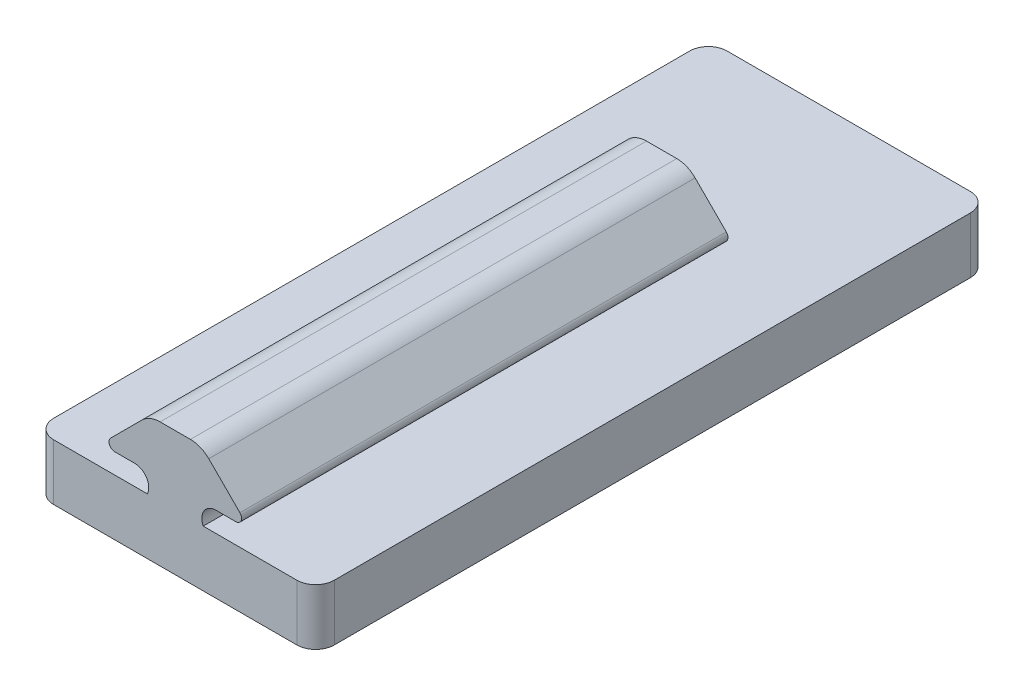
SolidWorks part; units mm, degrees
ref_plane "Front Plane" through (0, 0, 0) normal (0, 0, 1) x (1, 0, 0)
ref_plane "Top Plane" through (0, 0, 0) normal (0, 1, 0) x (1, 0, 0)
ref_plane "Right Plane" through (0, 0, 0) normal (1, 0, 0) x (0, 0, -1)
sketch "Sketch1" plane through (0, 0, 0) normal (0, 1, 0) x (1, 0, 0)
  line L1 (-13, 36) -> (13, 36)
  line L2 (-15, 34) -> (-15, -34)
  line L3 (-13, -36) -> (13, -36)
  line L4 (15, 34) -> (15, -34)
  line L5 (-15, 36) -> (15, -36) construction
  line L6 (-15, -36) -> (15, 36) construction
  arc A0 (13, 36) -> (15, 34) centre (13, 34) cw
  arc A1 (13, -36) -> (15, -34) centre (13, -34) ccw
  arc A2 (-15, -34) -> (-13, -36) centre (-13, -34) ccw
  arc A3 (-13, 36) -> (-15, 34) centre (-13, 34) ccw
  point P0 (0, 0)
  dimension "D1" = 2
  dimension "D2" = 72
  dimension "D3" = 30
extrude "Boss-Extrude1" add sketch "Sketch1" along normal blind 6
sketch "Sketch2" plane through (0, 0, 0) normal (0, 1, 0) x (1, 0, 0)
  line L0 (0, 24) -> (0, -24) construction
  circle A0 centre (0, 24) radius 4
  circle A1 centre (0, -24) radius 4
  point P3 (0, 0)
  dimension "D1" = 8
  dimension "D2" = 48
extrude "Cut-Extrude1" cut sketch "Sketch2" along normal blind 2
sketch "Sketch3" plane through (0, 0, 0) normal (0, 0, 1) x (1, 0, 0)
  line L0 (-5.3171, 5.6) -> (-5.3171, 3.6) construction
  line L1 (-5.3171, 3.6) -> (5.3171, 3.6) construction
  line L2 (5.3171, 3.6) -> (5.3171, 5.6) construction
  line L3 (-4.9167, 5.1447) -> (-4.343, 5.1447)
  line L4 (-4.343, 8.1545) -> (-6.4744, 8.1545)
  line L5 (-6.91, 9.206) -> (-3.5799, 12.5361)
  line L6 (-1.6177, 13.3489) -> (1.6185, 13.3489)
  line L7 (3.5807, 12.5361) -> (6.9108, 9.206)
  line L8 (6.4752, 8.1545) -> (4.3438, 8.1545)
  line L9 (4.3438, 5.1447) -> (4.9175, 5.1447)
  line L10 (4.9175, 3.9447) -> (4.9175, 5.1447)
  line L11 (-4.9167, 3.9447) -> (4.9175, 3.9447)
  line L12 (-4.9167, 5.1447) -> (-4.9167, 3.9447)
  line L13 (-5.3171, 5.6) -> (-4.3434, 5.6) construction
  line L14 (-4.3434, 7.8098) -> (-6.4748, 7.8098) construction
  line L15 (-7.1932, 9.5442) -> (-3.8632, 12.8743) construction
  line L16 (-1.6181, 13.8042) -> (1.6181, 13.8042) construction
  line L17 (3.8632, 12.8743) -> (7.1932, 9.5442) construction
  line L18 (6.4748, 7.8098) -> (4.3434, 7.8098) construction
  line L19 (4.3434, 5.6) -> (5.3171, 5.6) construction
  line L20 (-13, 6) -> (13, 6) construction
  line L21 (-13, 6) -> (13, 6)
  line L23 (4.9175, 3.9447) -> (10.9175, 3.9447)
  line L24 (4.9175, 3.9447) -> (4.9175, 5.1447)
  line L25 (4.9175, 5.1447) -> (10.9175, 5.1447)
  line L26 (10.9175, 3.9447) -> (10.9175, 5.1447)
  line L27 (-4.9167, 3.9447) -> (-10.9167, 3.9447)
  line L28 (-4.9167, 3.9447) -> (-4.9167, 5.1447)
  line L29 (-4.9167, 5.1447) -> (-10.9167, 5.1447)
  line L30 (-10.9167, 3.9447) -> (-10.9167, 5.1447)
  arc A0 (-4.343, 5.1447) -> (-4.343, 8.1545) centre (-4.343, 6.6496) ccw
  arc A1 (-6.91, 9.206) -> (-6.4744, 8.1545) centre (-6.4744, 8.7705) ccw
  arc A2 (-1.6177, 13.3489) -> (-3.5799, 12.5361) centre (-1.6177, 10.5739) ccw
  arc A3 (3.5807, 12.5361) -> (1.6185, 13.3489) centre (1.6185, 10.5739) ccw
  arc A4 (6.4752, 8.1545) -> (6.9108, 9.206) centre (6.4752, 8.7705) ccw
  arc A5 (4.3438, 8.1545) -> (4.3438, 5.1447) centre (4.3438, 6.6496) ccw
  arc A6 (-4.3434, 5.6) -> (-4.3434, 7.8098) centre (-4.3434, 6.7049) ccw construction
  arc A7 (-7.1932, 9.5442) -> (-6.4748, 7.8098) centre (-6.4748, 8.8258) ccw construction
  arc A8 (-1.6181, 13.8042) -> (-3.8632, 12.8743) centre (-1.6181, 10.6292) ccw construction
  arc A9 (3.8632, 12.8743) -> (1.6181, 13.8042) centre (1.6181, 10.6292) ccw construction
  arc A10 (6.4748, 7.8098) -> (7.1932, 9.5442) centre (6.4748, 8.8258) ccw construction
  arc A11 (4.3434, 7.8098) -> (4.3434, 5.6) centre (4.3434, 6.7049) ccw construction
  dimension "D1" = 2
  dimension "D2" = 6
extrude "Boss-Extrude2" add sketch "Sketch3" along normal up to surface (36 mm away) and the other way blind 16 contours L3 A0 L4 A1 L5 A2 L6 A3 L7 A4 L8 A5 L9 L10 L11 L12 | L24 L23 L26 L25 | L28 L27 L30 L29 up to face at (0, 3, 36)
